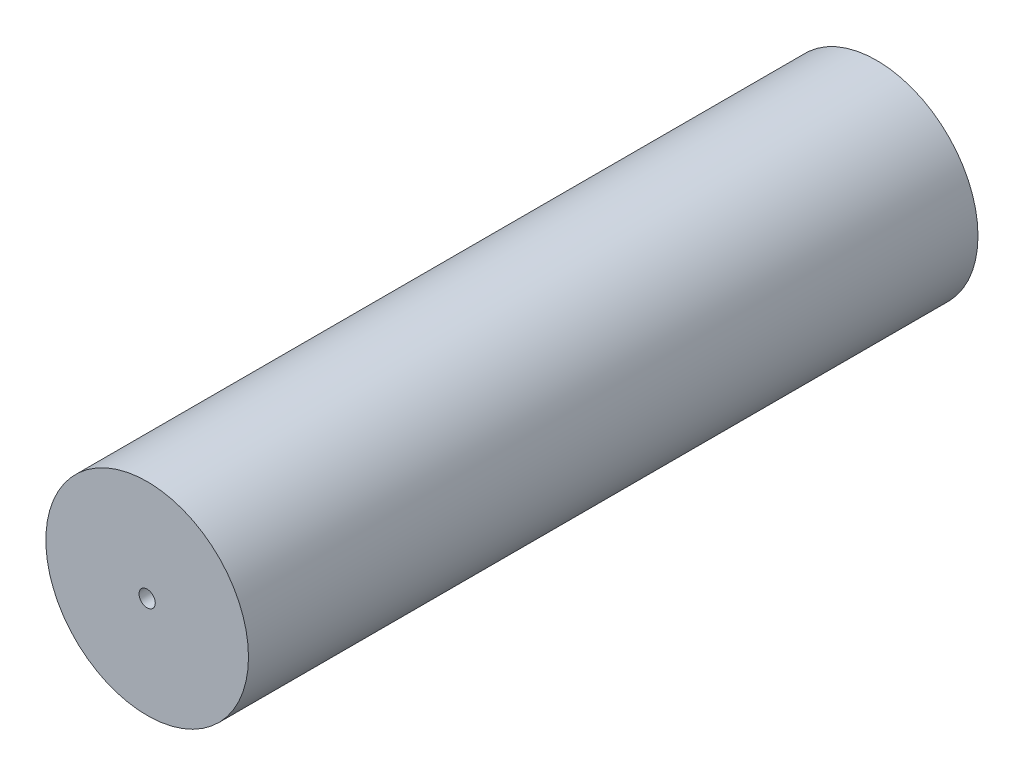
SolidWorks part; units mm, degrees
ref_plane "Front Plane" through (0, 0, 0) normal (0, 0, 1) x (1, 0, 0)
ref_plane "Top Plane" through (0, 0, 0) normal (0, 1, 0) x (1, 0, 0)
ref_plane "Right Plane" through (0, 0, 0) normal (1, 0, 0) x (0, 0, -1)
sketch "Sketch1" plane through (0, 0, 0) normal (0, 0, 1) x (1, 0, 0)
  circle A0 centre (0, 0) radius 125
  dimension "D1" = 250
extrude "Boss-Extrude1" add sketch "Sketch1" along normal blind 900
sketch "Sketch2" plane through (0, 0, 900) normal (0, 0, 1) x (1, 0, 0)
  circle A0 centre (0, 0) radius 10
  dimension "D1" = 20
extrude "Cut-Extrude1" cut sketch "Sketch2" against normal blind 350
sketch "Sketch3" plane through (0, 0, 0) normal (0, 0, -1) x (-1, 0, 0)
  circle A0 centre (0, 0) radius 10 construction
  circle A1 centre (0, 0) radius 10
extrude "Cut-Extrude2" cut sketch "Sketch3" against normal blind 400
